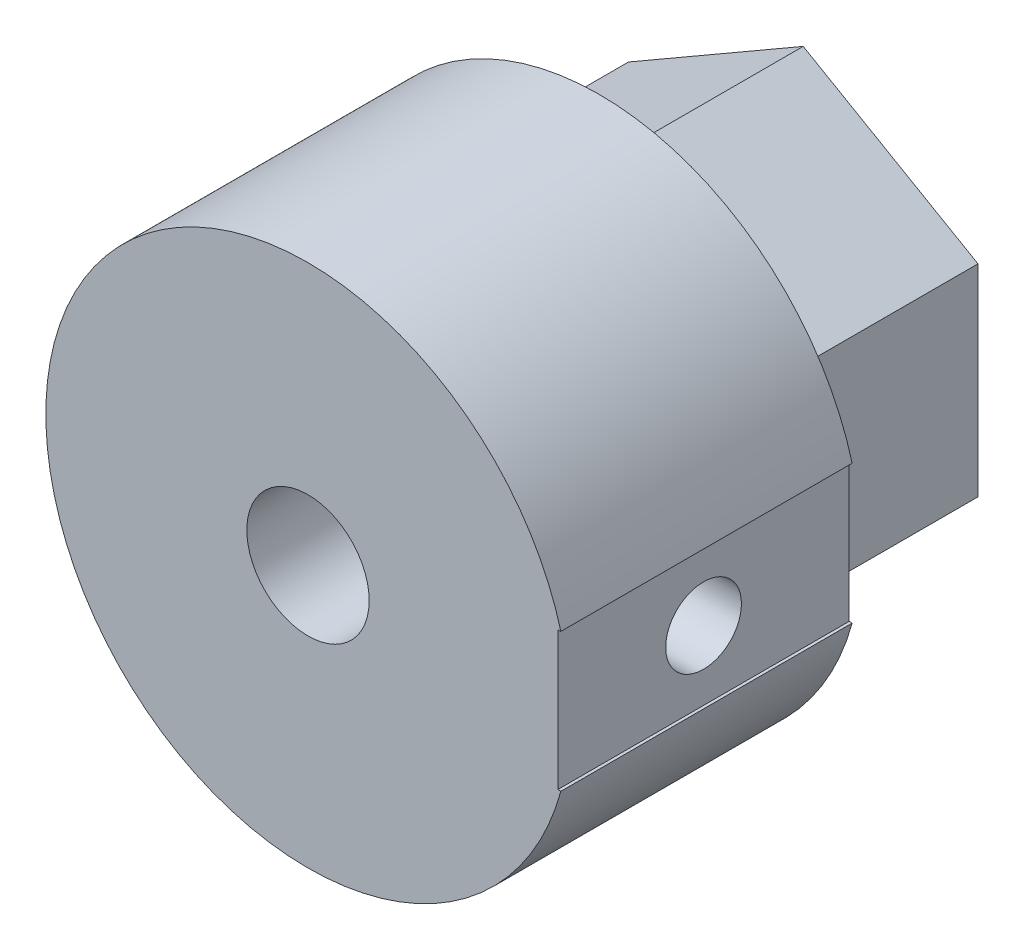
SolidWorks part; units mm, degrees
ref_plane "Plan de face" through (0, 0, 0) normal (0, 0, 1) x (1, 0, 0)
ref_plane "Plan de dessus" through (0, 0, 0) normal (0, 1, 0) x (1, 0, 0)
ref_plane "Plan de droite" through (0, 0, 0) normal (1, 0, 0) x (0, 0, -1)
sketch "Esquisse1" plane through (0, 0, 0) normal (0, 0, 1) x (1, 0, 0)
  line L1 (6, 3.4641) -> (0, 6.9282)
  line L2 (0, 6.9282) -> (-6, 3.4641)
  line L3 (-6, 3.4641) -> (-6, -3.4641)
  line L4 (-6, -3.4641) -> (0, -6.9282)
  line L5 (0, -6.9282) -> (6, -3.4641)
  line L6 (6, -3.4641) -> (6, 3.4641)
  circle A0 centre (0, 0) radius 6 construction
extrude "Boss.-Extru.1" add sketch "Esquisse1" along normal blind 17
sketch "Esquisse2" plane through (0, 0, 17) normal (0, 0, 1) x (1, 0, 0)
  circle A0 centre (0, 0) radius 1.3
extrude "Enlèv. mat.-Extru.1" cut sketch "Esquisse2" against normal blind 17
sketch "Esquisse3" plane through (0, 0, 17) normal (0, 0, 1) x (1, 0, 0)
  circle A0 centre (0, 0) radius 1.3
  circle A1 centre (0, 0) radius 9
extrude "Boss.-Extru.2" add sketch "Esquisse3" against normal blind 10
sketch "Esquisse4" plane through (0, 0, 17) normal (0, 0, 1) x (1, 0, 0)
  line L0 (9, 0) -> (-9, 0) construction
  line L2 (8.5787, -2.3757) -> (9.4213, -2.3757)
  line L3 (8.5787, -2.3757) -> (8.5787, 2.3757)
  line L4 (8.5787, 2.3757) -> (9.4213, 2.3757)
  line L5 (9.4213, -2.3757) -> (9.4213, 2.3757)
  line L6 (8.5787, -2.3757) -> (9.4213, 2.3757) construction
  line L7 (8.5787, 2.3757) -> (9.4213, -2.3757) construction
  circle A0 centre (0, 0) radius 9 construction
extrude "Enlèv. mat.-Extru.2" cut sketch "Esquisse4" against normal blind 12
sketch "Esquisse5" plane through (8.5787, 0, 0) normal (1, 0, 0) x (0, 0, -1)
  line L0 (-17, 0) -> (-7, 0) construction
  line L1 (-17, 2.3757) -> (-17, -2.3757) construction
  line L2 (-7, 2.3757) -> (-7, -2.3757) construction
  circle A0 centre (-12, 0) radius 1.3
extrude "Enlèv. mat.-Extru.3" cut sketch "Esquisse5" against normal blind 27
sketch "Esquisse6" plane through (0, 0, 17) normal (0, 0, 1) x (1, 0, 0)
  circle A0 centre (0, 0) radius 2.1
extrude "Enlèv. mat.-Extru.4" cut sketch "Esquisse6" against normal blind 10
